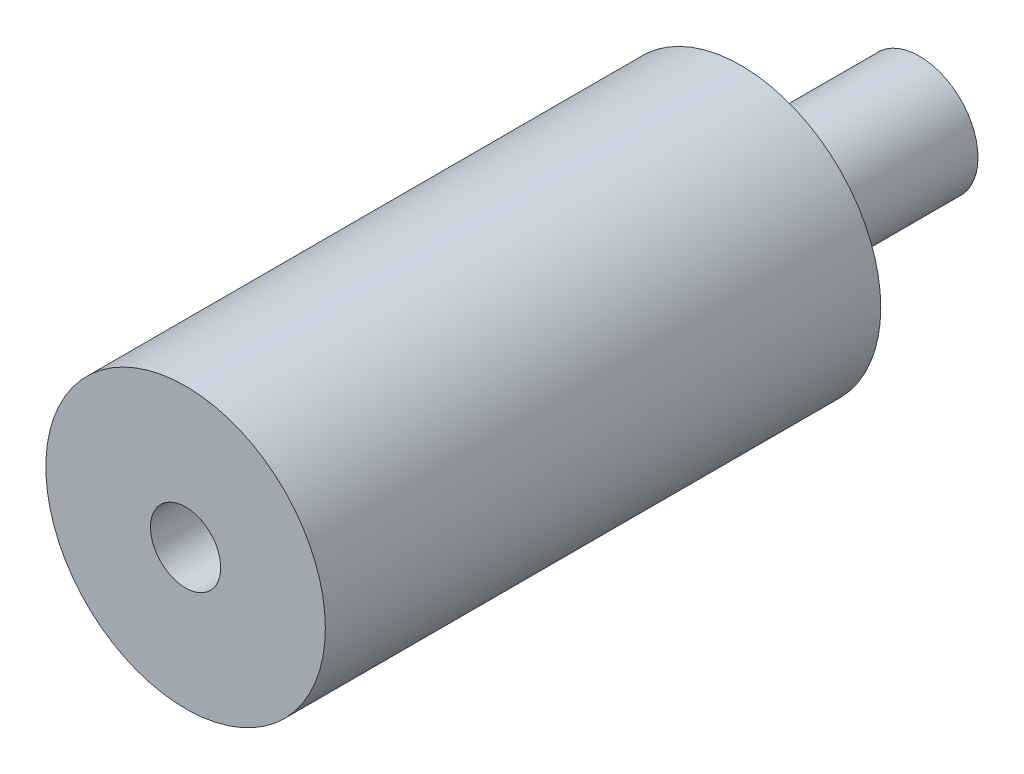
SolidWorks part; units mm, degrees
ref_plane "Front Plane" through (0, 0, 0) normal (0, 0, 1) x (1, 0, 0)
ref_plane "Top Plane" through (0, 0, 0) normal (0, 1, 0) x (1, 0, 0)
ref_plane "Right Plane" through (0, 0, 0) normal (1, 0, 0) x (0, 0, -1)
sketch "Sketch1" plane through (0, 0, 0) normal (0, 0, 1) x (1, 0, 0)
  circle A0 centre (0, 0) radius 5.969
  circle A1 centre (0, 0) radius 1.5
  dimension "D1" = 11.938
  dimension "D2" = 3
extrude "Extrude1" add sketch "Sketch1" along normal blind 23.7236
sketch "Sketch2" plane through (0, 0, 0) normal (0, 0, -1) x (-1, 0, 0)
  circle A0 centre (0, 0) radius 1.5 construction
  circle A1 centre (0, 0) radius 1.5
  circle A2 centre (0, 0) radius 2.5019
  dimension "D1" = 5.0038
extrude "Extrude2" add sketch "Sketch2" along normal blind 7.62
